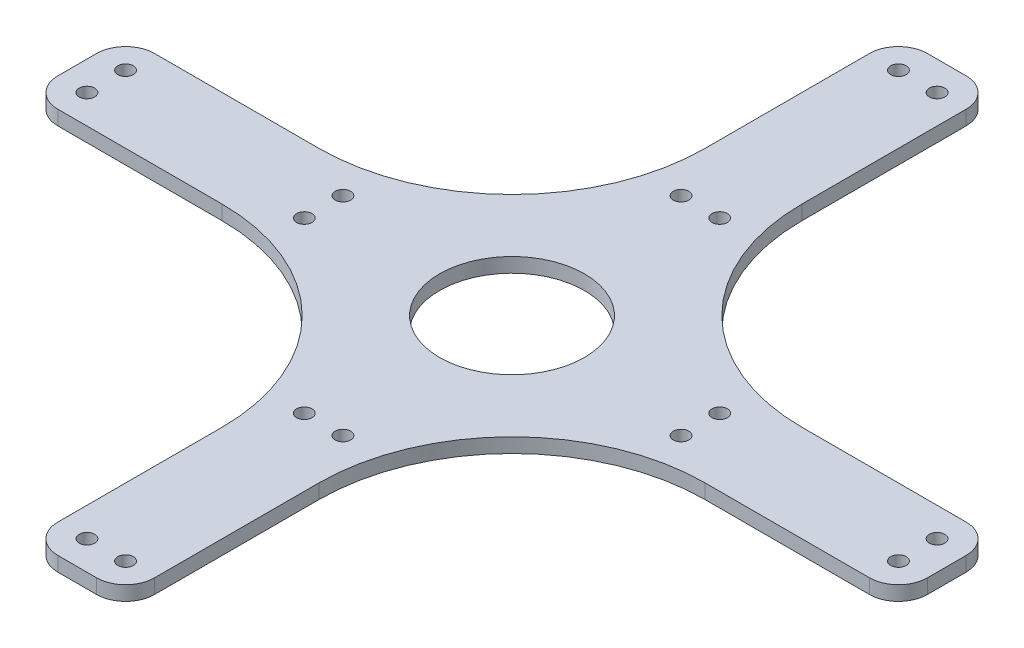
SolidWorks part; units mm, degrees
material "PLA"
ref_plane "Front Plane" through (0, 0, 0) normal (0, 0, 1) x (1, 0, 0)
ref_plane "Top Plane" through (0, 0, 0) normal (0, 1, 0) x (1, 0, 0)
ref_plane "Right Plane" through (0, 0, 0) normal (1, 0, 0) x (0, 0, -1)
sketch "Sketch1" plane through (0, 0, 0) normal (0, 1, 0) x (1, 0, 0)
  line L0 (0, 90) -> (0, -90) construction
  line L1 (-90, 0) -> (90, 0) construction
  line L2 (50, 10) -> (84, 10)
  line L3 (4, 90) -> (-4, 90)
  line L4 (10, 84) -> (10, 50)
  line L5 (4, -90) -> (-4, -90)
  line L6 (-10, 84) -> (-10, 50)
  line L7 (-84, 10) -> (-50, 10)
  line L8 (-90, 4) -> (-90, -4)
  line L9 (-84, -10) -> (-50, -10)
  line L10 (90, 4) -> (90, -4)
  line L11 (10, -50) -> (10, -84)
  line L12 (50, -10) -> (84, -10)
  line L13 (-10, -50) -> (-10, -84)
  arc A0 (4, 90) -> (10, 84) centre (4, 84) cw
  arc A1 (-4, 90) -> (-10, 84) centre (-4, 84) ccw
  arc A2 (84, 10) -> (90, 4) centre (84, 4) cw
  arc A3 (84, -10) -> (90, -4) centre (84, -4) ccw
  arc A4 (10, -84) -> (4, -90) centre (4, -84) cw
  arc A5 (-4, -90) -> (-10, -84) centre (-4, -84) cw
  arc A6 (-90, -4) -> (-84, -10) centre (-84, -4) ccw
  arc A7 (-84, 10) -> (-90, 4) centre (-84, 4) ccw
  arc A8 (50, 10) -> (10, 50) centre (50, 50) cw
  arc A9 (10, -50) -> (50, -10) centre (50, -50) cw
  arc A10 (-50, -10) -> (-10, -50) centre (-50, -50) cw
  arc A11 (-10, 50) -> (-50, 10) centre (-50, 50) cw
  point P5 (0, 0)
  point P8 (0, 0)
  point P16 (0, 90)
  point P23 (10, 90)
  point P26 (-10, 90)
  point P43 (10, -10)
  point P46 (-10, -10)
  dimension "D1" = 20
  dimension "D3" = 6
  dimension "D4" = 40
  dimension "D2" = 180
extrude "Boss-Extrude1" add sketch "Sketch1" along normal mid plane 3
hole_wizard "M3 Clearance Hole1" positions "Sketch3" profile "Sketch4" hole size "M3" standard "ANSI Metric" end condition up to next
sketch "Sketch3" plane through (0, 1.5, 0) normal (0, 1, 0) x (1, 0, 0)
  line L2 (-84, 4) -> (-39, 4) construction
  line L3 (-84, 4) -> (-84, -4) construction
  line L4 (-84, -4) -> (-39, -4) construction
  line L5 (-39, 4) -> (-39, -4) construction
  line L7 (-4, 84) -> (4, 84) construction
  line L8 (-4, 84) -> (-4, 39) construction
  line L9 (-4, 39) -> (4, 39) construction
  line L10 (4, 84) -> (4, 39) construction
  line L12 (39, 4) -> (84, 4) construction
  line L13 (39, 4) -> (39, -4) construction
  line L14 (39, -4) -> (84, -4) construction
  line L15 (84, 4) -> (84, -4) construction
  line L17 (-4, -39) -> (4, -39) construction
  line L18 (-4, -39) -> (-4, -84) construction
  line L19 (-4, -84) -> (4, -84) construction
  line L20 (4, -39) -> (4, -84) construction
  point P0 (-84, 4)
  point P3 (-84, -4)
  point P6 (-4, 84)
  point P9 (4, 84)
  point P12 (84, 4)
  point P15 (84, -4)
  point P18 (4, -84)
  point P21 (-4, -84)
  point P24 (-39, 4)
  point P26 (-39, -4)
  point P28 (39, 4)
  point P30 (39, -4)
  point P32 (4, -39)
  point P34 (-4, -39)
  point P36 (-4, 39)
  point P38 (4, 39)
  point P235 (0, 0)
  dimension "D1" = 45
sketch "Sketch4" plane through (-84, 1.5, -4) normal (1, 0, 0) x (0, 0, 1)
  line L0 (0, 0) -> (0, 3)
  line L1 (0, 3) -> (1.6, 3)
  line L2 (1.6, 3) -> (1.6, 0)
  line L5 (1.6, 0) -> (0, 0)
  line L11 (0, -6.35) -> (0, 107.95) construction
  dimension "Thru Hole Dia." = 3.2
  dimension "Thru Hole Depth" = 3
sketch "Sketch5" plane through (0, 1.5, 0) normal (0, 1, 0) x (1, 0, 0)
  circle A0 centre (0, 0) radius 15
  dimension "D1" = 30
extrude "Cut-Extrude1" cut sketch "Sketch5" against normal through all both and the other way through all
